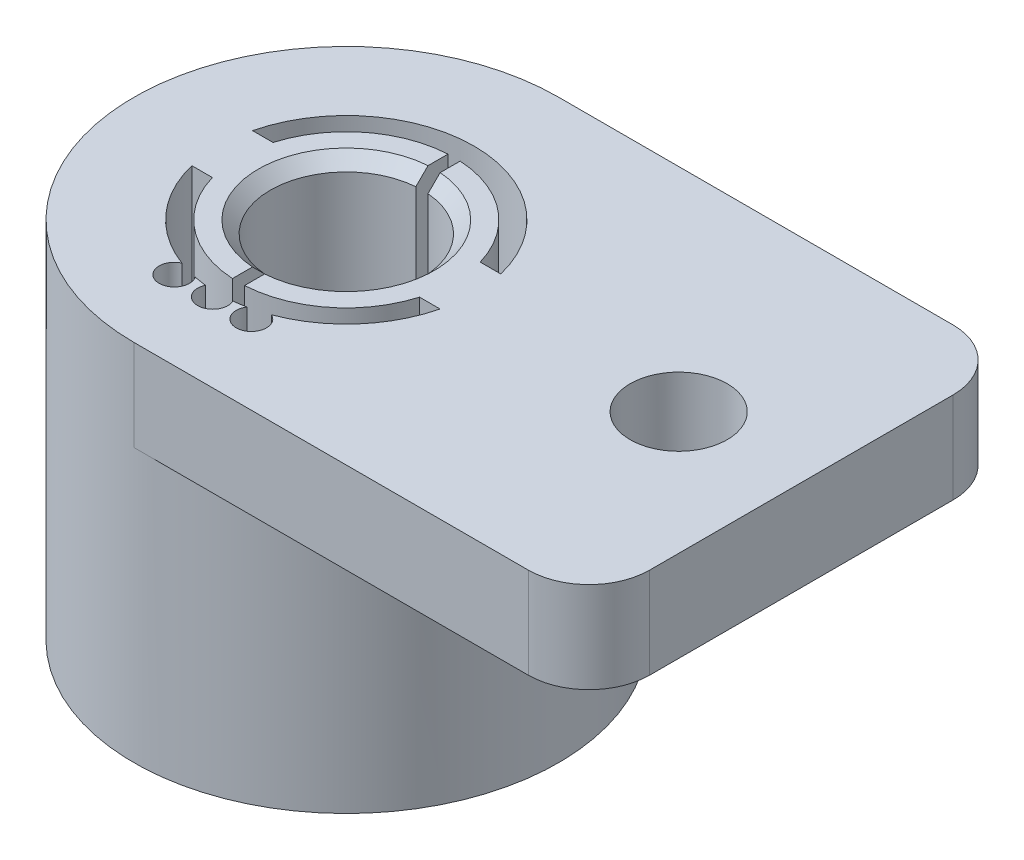
SolidWorks part; units mm, degrees
ref_plane "Спереди" through (0, 0, 0) normal (0, 0, 1) x (1, 0, 0)
ref_plane "Сверху" through (0, 0, 0) normal (0, 1, 0) x (1, 0, 0)
ref_plane "Справа" through (0, 0, 0) normal (1, 0, 0) x (0, 0, -1)
sketch "Эскиз1" plane through (0, 0, 0) normal (0, 1, 0) x (1, 0, 0)
  circle A0 centre (0, 0) radius 7
extrude "Бобышка-Вытянуть1" add sketch "Эскиз1" along normal blind 10
sketch "Эскиз3" plane through (0, 10, 0) normal (0, 1, 0) x (1, 0, 0)
  line L1 (0, 7) -> (15, 7)
  line L3 (0, -7) -> (15, -7)
  line L4 (15, 7) -> (15, -7)
  arc A0 (0, 7) -> (0, -7) centre (0, 0) ccw
  dimension "D1" = 15
extrude "Бобышка-Вытянуть2" add sketch "Эскиз3" along normal blind 3
sketch "Эскиз4" plane through (0, 0, 0) normal (0, -1, 0) x (1, 0, 0)
  circle A0 centre (0, 0) radius 2.5
extrude "Вырез-Вытянуть1" cut sketch "Эскиз4" against normal through all both and the other way through all
sketch "Эскиз6" plane through (0, 0, 0) normal (0, -1, 0) x (1, 0, 0)
  circle A0 centre (0, 0) radius 5.5855
  circle A1 centre (0, 0) radius 7
extrude "Вырез-Вытянуть3" cut sketch "Эскиз6" against normal blind 1
sketch "Эскиз7" plane through (0, 0, 0) normal (0, -1, 0) x (1, 0, 0)
  line L0 (3.4145, 1) -> (4.0917, 1)
  line L2 (-0.2, 3.5523) -> (-0.2, -3.5523)
  line L4 (0.2, 3.5523) -> (0.2, -3.5523)
  line L5 (-4.0917, 1) -> (-3.4145, 1)
  line L7 (-4.0917, -1) -> (-3.4145, -1)
  line L9 (3.4145, -1) -> (4.0917, -1)
  arc A0 (0.2, -3.5523) -> (3.4145, -1) centre (0, 0) ccw
  arc A1 (4.0917, 1) -> (-4.0917, 1) centre (0, 0) ccw
  arc A2 (-0.2, 3.5523) -> (-3.4145, 1) centre (0, 0) ccw
  arc A3 (3.4145, 1) -> (0.2, 3.5523) centre (0, 0) ccw
  arc A4 (-3.4145, -1) -> (-0.2, -3.5523) centre (0, 0) ccw
  arc A5 (-4.0917, -1) -> (4.0917, -1) centre (0, 0) ccw
  dimension "D1" = 0.4
extrude "Вырез-Вытянуть6" cut sketch "Эскиз7" against normal through all both and the other way through all
sketch "Эскиз8" plane through (0, 0, 0) normal (0, -1, 0) x (1, 0, 0)
  line L0 (-2.2806, 4.4) -> (2.3841, 4.4) construction
  circle A0 centre (0, 4.4) radius 0.5
  circle A1 centre (1.27, 4.4) radius 0.5
  circle A2 centre (-1.27, 4.4) radius 0.5
  point P2 (0, 0)
  point P3 (0, 0)
  dimension "D3" = 1.27
  dimension "D1" = 4.4
  dimension "D4" = 1.27
extrude "Вырез-под ножки" cut sketch "Эскиз8" against normal through all both and the other way through all
sketch "Эскиз9" plane through (0, 0, 0) normal (0, -1, 0) x (1, 0, 0)
  line L1 (-2.25, 5.6736) -> (2.25, 5.6736)
  line L2 (-2.25, 5.6736) -> (-2.25, 3.6804)
  line L3 (-2.25, 3.6804) -> (2.25, 3.6804)
  line L4 (2.25, 5.6736) -> (2.25, 3.6804)
  point P5 (0, 3.6804)
  dimension "D1" = 4.5
extrude "Вырез под TSSOP" cut sketch "Эскиз9" against normal blind 2
fillet "Скругление1" radius 2 2 edges at (15, 11.5, -7) (15, 11.5, 7)
sketch "Эскиз10" plane through (0, 10, 0) normal (0, -1, 0) x (1, 0, 0)
  circle A0 centre (10.9563, 0) radius 1.6
extrude "Вырез-Вытянуть9" cut sketch "Эскиз10" against normal through all both and the other way through all
sketch "Эскиз11" plane through (0, 0, 0) normal (0, -1, 0) x (1, 0, 0)
  circle A0 centre (0, 0) radius 4.7855
  arc A1 (-2.25, 5.1123) -> (2.25, 5.1123) centre (0, 0) ccw construction
  dimension "D1" = 0.8
extrude "Вырез-Вытянуть10" cut sketch "Эскиз11" against normal blind 0.5
chamfer "Фаска1" distance 0.4 angle 45 1 edges at (0, 0, -5.5855)
chamfer "Фаска2" distance 0.4 angle 45 1 edges at (2.5, 0.5, 0)
chamfer "Фаска3" distance 0.4 angle 45 2 edges at (2.5, 13, 0) (-2.5, 13, 0)
chamfer "Фаска4" distance 0.4 angle 45 1 edges at (-2.5, 0.5, 0)
